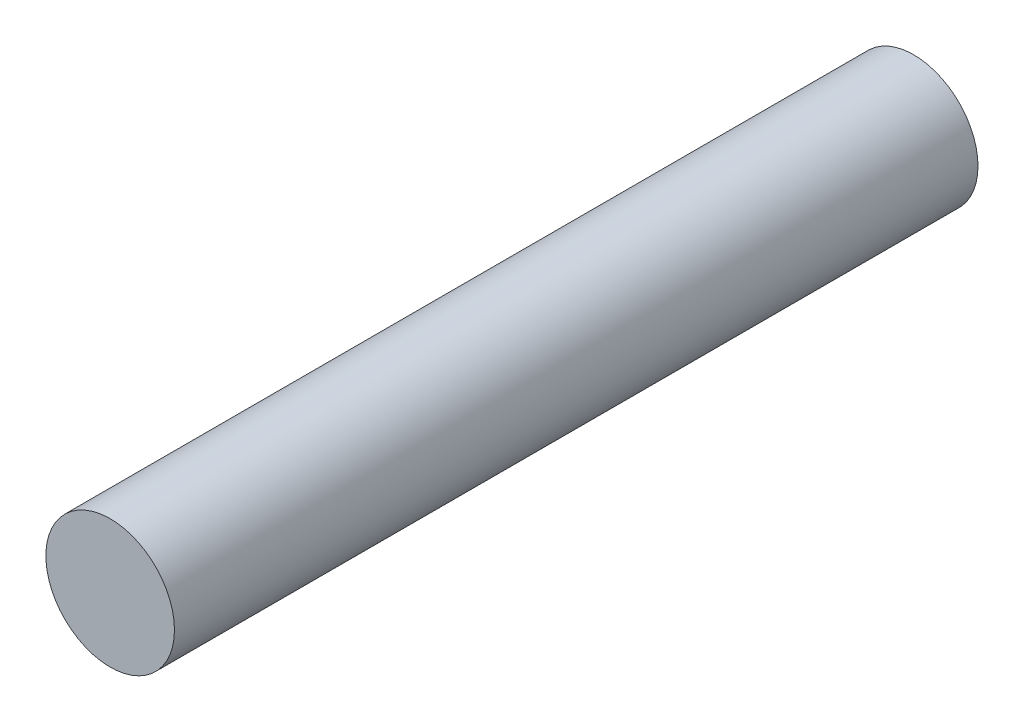
SolidWorks part; units mm, degrees
material "AISI 304"
ref_plane "前基準面" through (0, 0, 0) normal (0, 0, 1) x (1, 0, 0)
ref_plane "上基準面" through (0, 0, 0) normal (0, 1, 0) x (1, 0, 0)
ref_plane "右基準面" through (0, 0, 0) normal (1, 0, 0) x (0, 0, -1)
sketch "草圖1" plane through (0, 0, 0) normal (0, 0, 1) x (1, 0, 0)
  circle A0 centre (0, 0) radius 4
  dimension "D1" = 8
extrude "填料-伸長1" add sketch "草圖1" along normal blind 50
